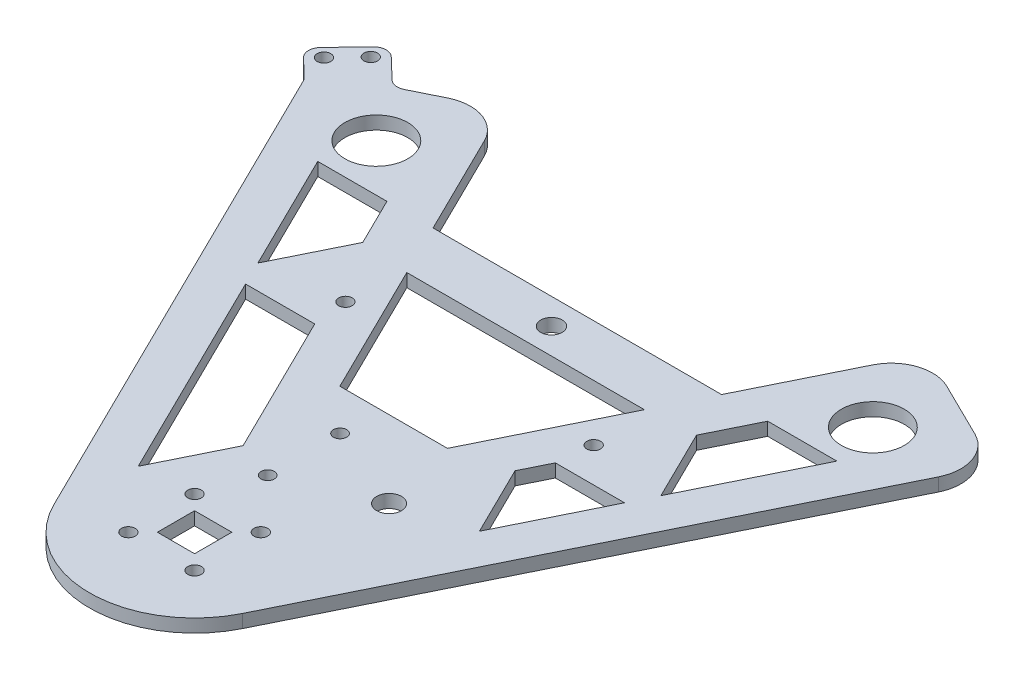
SolidWorks part; units mm, degrees
ref_plane "Front Plane" through (0, 0, 0) normal (0, 0, 1) x (1, 0, 0)
ref_plane "Top Plane" through (0, 0, 0) normal (0, 1, 0) x (1, 0, 0)
ref_plane "Right Plane" through (0, 0, 0) normal (1, 0, 0) x (0, 0, -1)
sketch "Sketch1" plane through (0, 0, 0) normal (0, 1, 0) x (1, 0, 0)
  line L0 (-60, 103.923) -> (60, 103.923) construction
  line L1 (-4.5, -4.5) -> (4.5, -4.5)
  line L2 (-4.5, -4.5) -> (-4.5, 4.5)
  line L3 (-4.5, 4.5) -> (4.5, 4.5)
  line L4 (4.5, -4.5) -> (4.5, 4.5)
  line L5 (-4.5, -4.5) -> (4.5, 4.5) construction
  line L6 (-4.5, 4.5) -> (4.5, -4.5) construction
  line L7 (-82.7138, 110.4306) -> (-22.7854, -11.2243)
  line L8 (22.7854, -11.2243) -> (82.7138, 110.4306)
  line L9 (-51.3166, 125.8972) -> (0, 21.7243)
  line L10 (0, 21.7243) -> (51.3166, 125.8972)
  line L11 (51.3166, 125.8972) -> (82.7138, 110.4306)
  line L12 (-82.7138, 110.4306) -> (-51.3166, 125.8972)
  line L13 (-57.5832, 99.017) -> (-36.1852, 55.5789) construction
  line L14 (-10.5973, -39.3898) -> (22084.5016, 44813.7774) construction
  line L15 (-13, 48.1143) -> (13, 48.1143)
  line L16 (17.5, 29.5105) -> (-3.1, 29.5105) construction
  line L17 (-8, -8) -> (8, -8) construction
  line L18 (-8, -8) -> (-8, 8) construction
  line L19 (-8, 8) -> (8, 8) construction
  line L20 (8, -8) -> (8, 8) construction
  line L21 (-8, -8) -> (8, 8) construction
  line L22 (-8, 8) -> (8, -8) construction
  line L23 (-3.1, 38.2605) -> (-3.1, 20.7605) construction
  line L24 (-30, 66.4531) -> (30, 66.4531) construction
  line L25 (-34.8648, 92.5) -> (34.8648, 92.5)
  line L26 (-28.7072, 80) -> (28.7072, 80)
  line L27 (0, 80) -> (0, 92.5) construction
  circle A0 centre (60, 103.923) radius 7.6
  circle A1 centre (-60, 103.923) radius 7.6
  arc A2 (22.7854, -11.2243) -> (-22.7854, -11.2243) centre (0, 0) cw
  circle A6 centre (-30, 66.4531) radius 1.65
  circle A7 centre (30, 66.4531) radius 1.65
  circle A8 centre (17.5, 29.5105) radius 3
  circle A9 centre (-8, 8) radius 1.65
  circle A10 centre (8, 8) radius 1.65
  circle A11 centre (8, -8) radius 1.65
  circle A12 centre (-8, -8) radius 1.65
  circle A13 centre (-3.1, 38.2605) radius 1.6
  circle A14 centre (-3.1, 20.7605) radius 1.6
  circle A15 centre (0, 86.25) radius 2.6
  point P4 (0, 0)
  point P10 (0, 103.923)
  point P19 (67.0152, 118.1639)
  point P20 (-67.0152, 118.1639)
  point P45 (0, 66.4531)
  point P49 (-3.1, 29.5105)
  point P56 (0, 86.25)
  dimension "D3" = 15.2
  dimension "D7" = 25.4
  dimension "D8" = 3.3
  dimension "D9" = 48
  dimension "D11" = 6
  dimension "D14" = 3.3
  dimension "D17" = 3.2
  dimension "D22" = 5.2
  dimension "D1" = 9
  dimension "D2" = 35
  dimension "D4" = 120
  dimension "D5" = 120
  dimension "D6" = 15.875
  dimension "D10" = 26
  dimension "D12" = 39
  dimension "D13" = 16
  dimension "D15" = 20.6
  dimension "D16" = 17.5
  dimension "D18" = 60
  dimension "D19" = 17.5
  dimension "D20" = 12.5
  dimension "D21" = 80
extrude "Boss-Extrude1" add sketch "Sketch1" along normal blind 3.175
fillet "Fillet1" radius 10 4 edges at (82.7138, 1.5875, -110.4306) (51.3166, 1.5875, -125.8972) (-51.3166, 1.5875, -125.8972) (-82.7138, 1.5875, -110.4306)
sketch "Sketch2" plane through (0, 3.175, 0) normal (0, 1, 0) x (1, 0, 0)
  line L0 (-45.7948, 58.1143) -> (-29.0736, 58.1143)
  line L1 (-29.0736, 58.1143) -> (-12.2548, 23.9721)
  line L2 (-12.2548, 23.9721) -> (-20.6154, 7)
  line L3 (-20.6154, 7) -> (-45.7948, 58.1143)
  line L8 (-62.7335, 92.5) -> (-48.6941, 64)
  line L9 (-48.6941, 64) -> (-40.3335, 80.9721)
  line L10 (-40.3335, 80.9721) -> (-46.0123, 92.5)
  line L11 (-46.0123, 92.5) -> (-62.7335, 92.5)
  line L12 (-78.2948, 101.46) -> (-22.7854, -11.2243) construction
  line L13 (-33.2051, 32.5572) -> (-42.1757, 28.1382) construction
  line L14 (-55.7138, 78.25) -> (-64.6845, 73.831) construction
  line L15 (-43.1729, 86.736) -> (-34.2023, 91.1551) construction
  line L16 (-20.6642, 41.0432) -> (-11.6935, 45.4622) construction
  line L17 (-28.7072, 80) -> (-13, 48.1143) construction
  line L18 (13, 48.1143) -> (28.7072, 80) construction
  line L19 (-28.7072, 80) -> (28.7072, 80) construction
  line L20 (-34.8648, 92.5) -> (34.8648, 92.5) construction
  line L21 (-13, 48.1143) -> (13, 48.1143) construction
  line L22 (29.0736, 58.1143) -> (45.7948, 58.1143)
  line L23 (45.7948, 58.1143) -> (34.2185, 34.6143)
  line L24 (34.2185, 34.6143) -> (25.8579, 51.5864)
  line L25 (25.8579, 51.5864) -> (29.0736, 58.1143)
  line L26 (46.0123, 92.5) -> (62.7335, 92.5)
  line L27 (62.7335, 92.5) -> (48.6941, 64)
  line L28 (48.6941, 64) -> (40.3335, 80.9721)
  line L29 (40.3335, 80.9721) -> (46.0123, 92.5)
  line L30 (22.7854, -11.2243) -> (78.2948, 101.46) construction
  line L31 (55.7138, 78.25) -> (64.6845, 73.831) construction
  line L32 (43.1729, 86.736) -> (34.2023, 91.1551) construction
  line L33 (34.8648, 92.5) -> (46.8976, 116.9266) construction
  dimension "D1" = 10
  dimension "D2" = 10
  dimension "D3" = 16
  dimension "D4" = 7
  dimension "D5" = 13.5
extrude "Cut-Extrude1" cut sketch "Sketch2" against normal through all both and the other way through all
sketch "Sketch3" plane through (0, 0, 0) normal (0, 1, 0) x (1, 0, 0)
  line L0 (-69.2579, 117.0592) -> (-77.9226, 125.3611)
  line L1 (-73.7432, 114.8497) -> (-60.2872, 121.4782) construction
  line L2 (-77.9226, 125.3611) -> (-88.3, 114.5301)
  line L3 (-88.3, 114.5301) -> (-81.545, 108.058)
  line L4 (-78.2948, 101.46) -> (-22.7854, -11.2243) construction
  line L5 (-83.7124, 114.9818) -> (-78.1778, 120.7584) construction
  line L6 (-83.1113, 119.9456) -> (-80.9451, 117.8701) construction
  line L7 (-81.545, 108.058) -> (-78.2948, 101.46)
  line L8 (-73.7432, 114.8497) -> (-69.2579, 117.0592)
  circle A0 centre (-78.1778, 120.7584) radius 1.65
  circle A1 centre (-83.7124, 114.9818) radius 1.65
  arc A2 (-78.2948, 101.46) -> (-73.7432, 114.8497) centre (-69.3241, 105.879) cw
  arc A3 (-73.7432, 114.8497) -> (-78.2948, 101.46) centre (-69.3241, 105.879) ccw construction
  dimension "D5" = 3.3
  dimension "D1" = 110
  dimension "D2" = 15
  dimension "D3" = 12
  dimension "D4" = 10
  dimension "D6" = 8
  dimension "D7" = 3
extrude "Boss-Extrude2" add sketch "Sketch3" along normal up to surface (3.175 mm away) up to face at (33.7362, 3.175, -50.6074)
fillet "Fillet2" radius 3 4 edges at (-88.3, 1.5875, -114.5301) (-77.9226, 1.5875, -125.3611) (-81.545, 1.5875, -108.058) (-69.2579, 1.5875, -117.0592)
